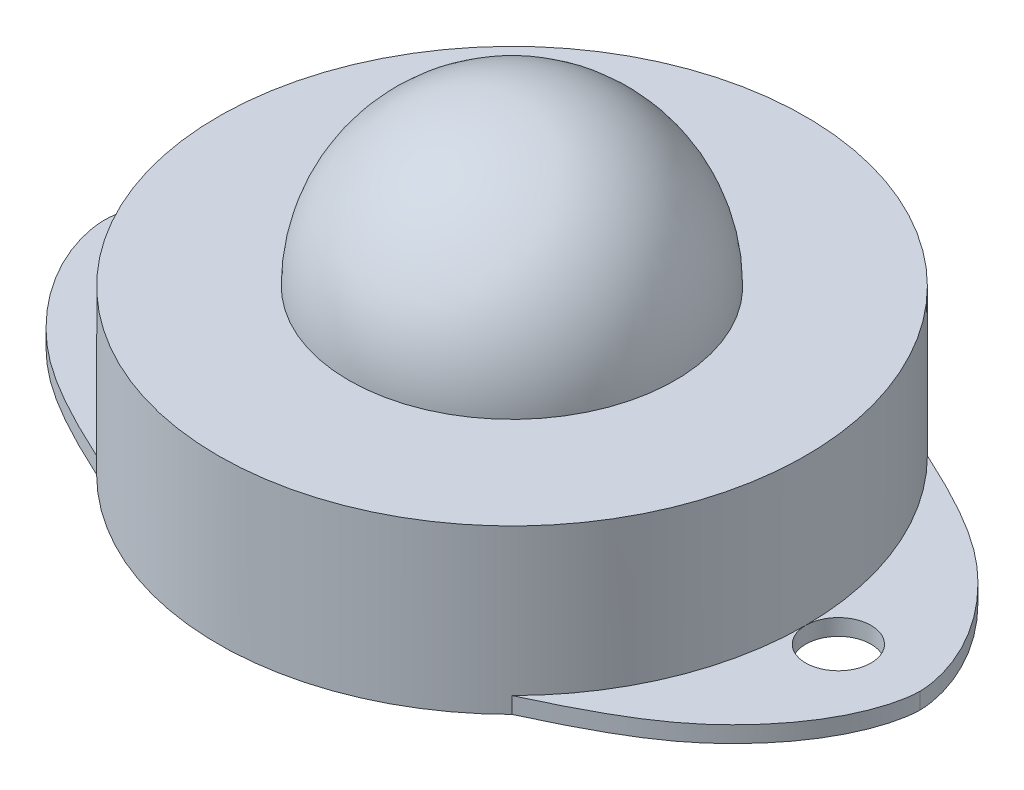
SolidWorks part; units mm, degrees
ref_plane "Front Plane" through (0, 0, 0) normal (0, 0, 1) x (1, 0, 0)
ref_plane "Top Plane" through (0, 0, 0) normal (0, 1, 0) x (1, 0, 0)
ref_plane "Right Plane" through (0, 0, 0) normal (1, 0, 0) x (0, 0, -1)
sketch "Sketch1" plane through (0, 0, 0) normal (0, 1, 0) x (1, 0, 0)
  line L0 (-48.9259, 0) -> (53.5671, 0) construction
  circle A0 centre (0, 0) radius 18
  dimension "D1" = 36
extrude "Boss-Extrude1" add sketch "Sketch1" along normal blind 10
sketch "Sketch2" plane through (0, 0, 0) normal (0, -1, 0) x (1, 0, 0)
  line L0 (-31.2422, 0) -> (6.4521, 0) construction
  line L1 (0, 26.4788) -> (0, -19.9401) construction
  line L2 (0, 0) -> (-24.0522, 24.0522) construction
  line L3 (-25, -1.0351) -> (-25, 1.0351) construction
  circle A0 centre (-20, 0) radius 2
  arc A1 (-24.8102, 1.3644) -> (-24.8102, -1.3644) centre (-20, 0) ccw
  circle A2 centre (0, 0) radius 18 construction
  arc A3 (-12.7279, 12.7279) -> (-12.7279, -12.7279) centre (0, 0) ccw
  circle A4 centre (-20, 0) radius 5 construction
  circle A5 centre (20, 0) radius 2
  arc A6 (12.7279, -12.7279) -> (12.7279, 12.7279) centre (0, 0) ccw
  spline S0 degree 3 poles (-12.7279, 12.7279) (-17.4135, 10.5789) (-23.9251, 5.7668) (-25, 1.2939) (-25, 0) knots 0 0 0 0 0.294967 1 1 1 1
  spline S1 degree 3 poles (-12.7279, -12.7279) (-17.4135, -10.5789) (-23.9251, -5.7668) (-25, -1.2939) (-25, 0) knots 0 0 0 0 0.294967 1 1 1 1
  spline S2 degree 3 poles (12.7279, 12.7279) (17.4135, 10.5789) (23.9251, 5.7668) (25, 1.2939) (25, 0) knots 0 0 0 0 0.294967 1 1 1 1
  spline S3 degree 3 poles (12.7279, -12.7279) (17.4135, -10.5789) (23.9251, -5.7668) (25, -1.2939) (25, 0) knots 0 0 0 0 0.294967 1 1 1 1
  dimension "D1" = 4
  dimension "D2" = 20
  dimension "D3" = 3
extrude "Boss-Extrude11" add sketch "Sketch2" against normal blind 1 contours S1 L1 A0 S0 | A0 | L1 S3 S2 A5 | A5
sketch "Sketch3" plane through (0, 0, 0) normal (0, -1, 0) x (1, 0, 0)
  circle A0 centre (-20, 0) radius 2 construction
  circle A1 centre (-20, 0) radius 2
  circle A2 centre (20, 0) radius 2 construction
  circle A3 centre (20, 0) radius 2
extrude "Cut-Extrude1" cut sketch "Sketch3" against normal blind 2
sketch "Sketch4" plane through (0, 10, 0) normal (0, 1, 0) x (1, 0, 0)
  line L0 (0, 19.9566) -> (0, -20.418) construction
  line L1 (0, 10) -> (0, -10)
  arc A0 (0, -10) -> (0, 10) centre (0, 0) ccw
  dimension "D1" = 20
revolve "Revolve1" add sketch "Sketch4" angle 360 about L0
